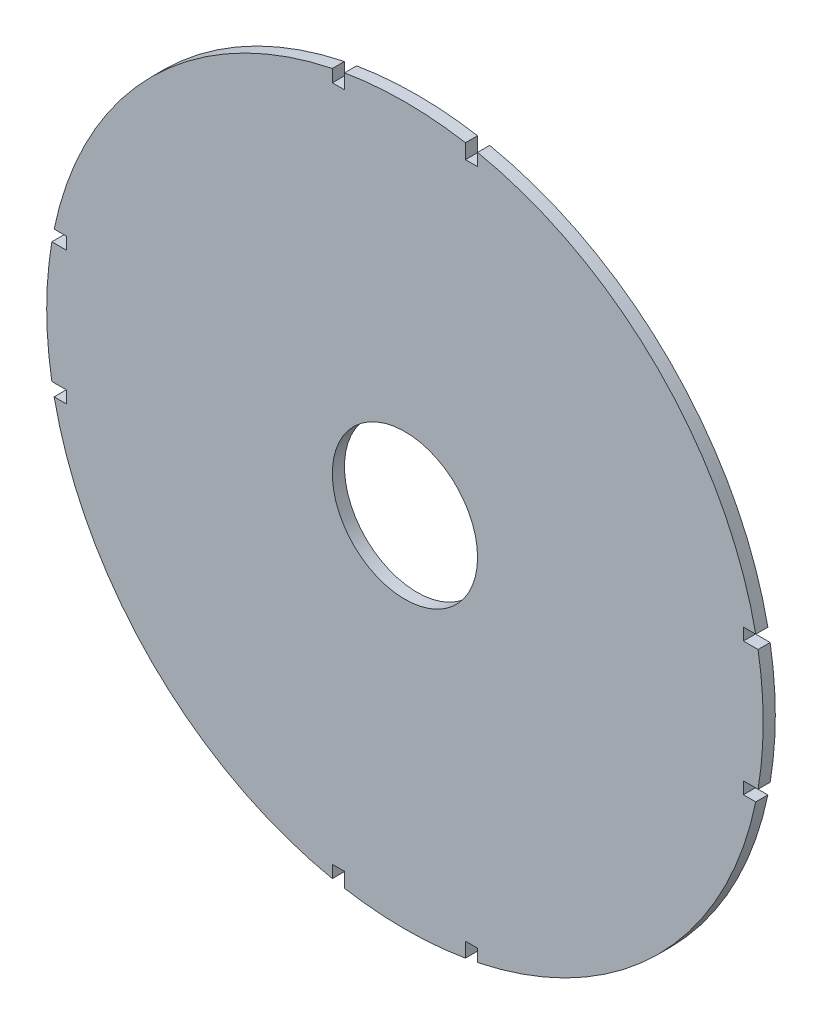
SolidWorks part; units mm, degrees
material "ABS"
ref_plane "Front Plane" through (0, 0, 0) normal (0, 0, 1) x (1, 0, 0)
ref_plane "Top Plane" through (0, 0, 0) normal (0, 1, 0) x (1, 0, 0)
ref_plane "Right Plane" through (0, 0, 0) normal (1, 0, 0) x (0, 0, -1)
sketch "Sketch1" plane through (0, 0, 0) normal (0, 0, 1) x (1, 0, 0)
  line L0 (-19.05, -88.7742) -> (-15.875, -88.7742)
  line L1 (-15.875, -88.7742) -> (-15.875, -92.6295)
  line L2 (19.05, 88.7742) -> (19.05, 92.029)
  line L3 (19.05, 88.7742) -> (15.875, 88.7742)
  line L4 (15.875, 88.7742) -> (15.875, 92.6295)
  line L5 (-19.05, 88.7742) -> (-19.05, 92.029)
  line L6 (-19.05, 88.7742) -> (-15.875, 88.7742)
  line L7 (-15.875, 88.7742) -> (-15.875, 92.6295)
  line L9 (19.05, -88.7742) -> (19.05, -92.029)
  line L10 (15.875, -88.7742) -> (15.875, -92.6295)
  line L11 (19.05, -88.7742) -> (15.875, -88.7742)
  line L12 (-19.05, -88.7742) -> (-19.05, -92.029)
  line L14 (88.7742, -19.05) -> (88.7742, -15.875)
  line L15 (88.7742, 15.875) -> (92.6295, 15.875)
  line L16 (88.7742, 19.05) -> (92.029, 19.05)
  line L17 (88.7742, 19.05) -> (88.7742, 15.875)
  line L18 (-88.7742, 19.05) -> (-92.029, 19.05)
  line L19 (-88.7742, 19.05) -> (-88.7742, 15.875)
  line L20 (88.7742, -19.05) -> (92.029, -19.05)
  line L21 (-88.7742, 15.875) -> (-92.6295, 15.875)
  line L22 (-88.7742, -15.875) -> (-92.6295, -15.875)
  line L23 (-88.7742, -19.05) -> (-92.029, -19.05)
  line L24 (-88.7742, -19.05) -> (-88.7742, -15.875)
  line L27 (88.7742, -15.875) -> (92.6295, -15.875)
  arc A0 (15.875, 92.6295) -> (-15.875, 92.6295) centre (0, 0) ccw
  arc A1 (-22.225, 91.3142) -> (-91.3142, 22.225) centre (0, 0) ccw
  arc A2 (92.029, 19.05) -> (19.05, 92.029) centre (0, 0) ccw
  arc A3 (92.6295, -15.875) -> (92.6295, 15.875) centre (0, 0) ccw
  arc A4 (-91.3142, 22.225) -> (-92.029, 19.05) centre (0, 0) ccw
  arc A5 (-92.029, -19.05) -> (-19.05, -92.029) centre (0, 0) ccw
  arc A6 (-15.875, -92.6295) -> (15.875, -92.6295) centre (0, 0) ccw
  arc A7 (22.225, -91.3142) -> (92.029, -19.05) centre (0, 0) ccw
  arc A8 (19.05, -92.029) -> (22.225, -91.3142) centre (0, 0) ccw
  arc A9 (-19.05, 92.029) -> (-22.225, 91.3142) centre (0, 0) ccw
  arc A10 (-92.6295, 15.875) -> (-92.6295, -15.875) centre (0, 0) ccw
  circle A11 centre (0, 0) radius 19.05
  point P49 (-69.85, 0)
  point P52 (0, -69.85)
  point P55 (69.85, 0)
  point P58 (0, 69.85)
  dimension "D1" = 3.175
  dimension "D3" = 38.1
  dimension "D2" = 3.175
extrude "Boss-Extrude1" add sketch "Sketch1" along normal blind 3.175
